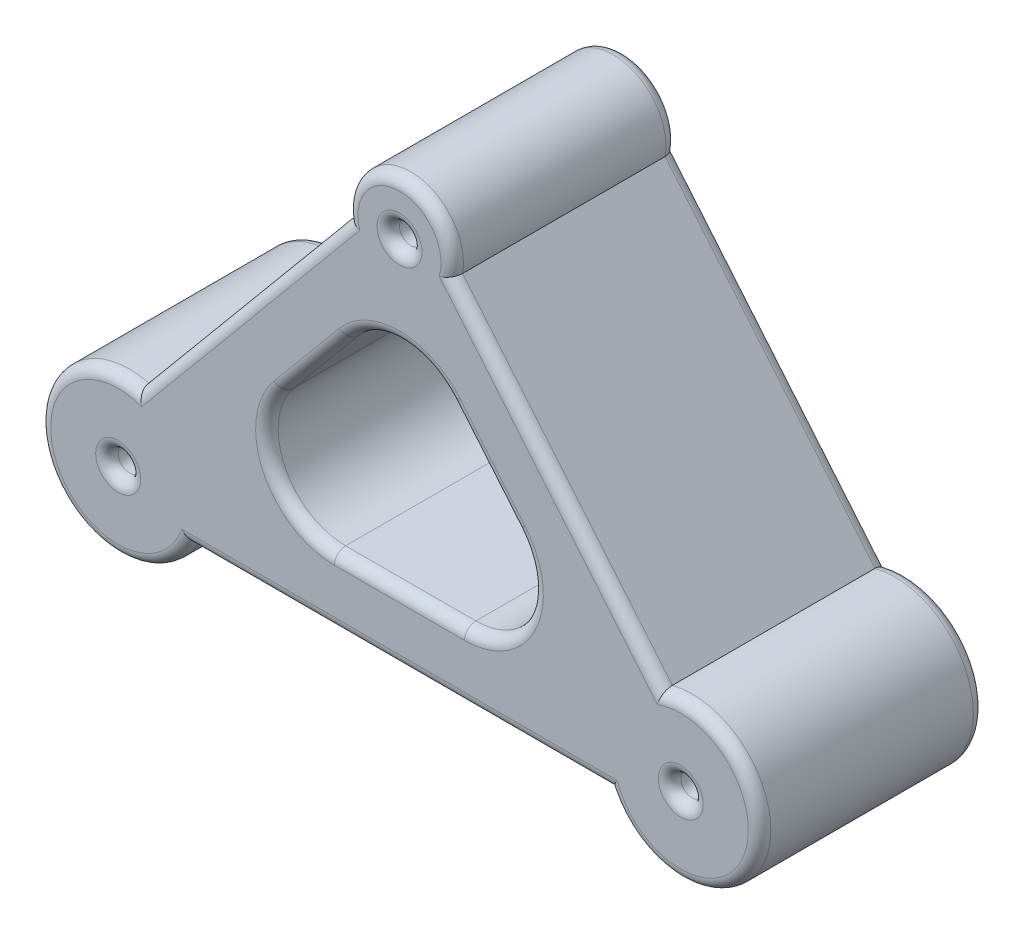
SolidWorks part; units mm, degrees
ref_plane "Front Plane" through (0, 0, 0) normal (0, 0, 1) x (1, 0, 0)
ref_plane "Top Plane" through (0, 0, 0) normal (0, 1, 0) x (1, 0, 0)
ref_plane "Right Plane" through (0, 0, 0) normal (1, 0, 0) x (0, 0, -1)
sketch "Esquisse1" plane through (0, 0, 0) normal (0, 0, 1) x (1, 0, 0)
  line L0 (0, 0) -> (0, 15) construction
  line L1 (-11.6279, 3.3896) -> (-2.3047, 14.5775)
  line L2 (-12.5, 0) -> (0, 15) construction
  line L3 (-5.197, 6.4206) -> (-2.3047, 9.8913)
  line L4 (-12.5, 0) -> (0, 0) construction
  line L5 (2.8923, 1.5) -> (-2.8923, 1.5)
  line L6 (9.3377, -1.5) -> (-9.3377, -1.5)
  line L7 (0, 15) -> (12.5, 0) construction
  line L8 (12.5, 0) -> (0, 0) construction
  line L9 (5.197, 6.4206) -> (2.3047, 9.8913)
  line L11 (2.3047, 14.5775) -> (11.6279, 3.3896)
  circle A0 centre (-12.5, 0) radius 0.5
  arc A2 (2.3047, 14.5775) -> (-2.3047, 14.5775) centre (0, 15) ccw
  circle A3 centre (0, 15) radius 0.5
  circle A5 centre (12.5, 0) radius 0.5
  arc A8 (-11.6279, 3.3896) -> (-9.3377, -1.5) centre (-12.5, 0) ccw
  arc A9 (2.8923, 1.5) -> (5.197, 6.4206) centre (2.8923, 4.5) ccw
  arc A10 (-2.8923, 1.5) -> (-5.197, 6.4206) centre (-2.8923, 4.5) cw
  arc A11 (-2.3047, 9.8913) -> (2.3047, 9.8913) centre (0, 7.9708) cw
  arc A12 (11.6279, 3.3896) -> (9.3377, -1.5) centre (12.5, 0) cw
  point P24 (0, 12.6569)
  dimension "D1" = 1
  dimension "D2" = 25
  dimension "D3" = 3.5
  dimension "D7" = 3
  dimension "D4" = 15
  dimension "D5" = 3
  dimension "D6" = 3
extrude "Boss.-Extru.1" add sketch "Esquisse1" along normal mid plane 10
fillet "Congé2" radius 0.5 30 edges at (13, 0, 5) (0.5, 15, 5) (3.7508, 8.1559, 5) (0, 10.9708, 5) (-3.7508, 8.1559, 5) (-5.6091, 3.2275, 5) (0, 1.5, 5) (5.6091, 3.2275, 5) (0, -1.5, 5) (-15.6696, -1.4845, 5) (-6.9663, 8.9835, 5) (0, 17.3431, 5) (6.9663, 8.9835, 5) (15.6696, -1.4845, 5) (-12, 0, 5) (13, 0, -5) (-5.6091, 3.2275, -5) (-3.7508, 8.1559, -5) (0, 10.9708, -5) (3.7508, 8.1559, -5) (5.6091, 3.2275, -5) (0, 1.5, -5) (-12, 0, -5) (6.9663, 8.9835, -5) (0, 17.3431, -5) (-6.9663, 8.9835, -5) (-15.6696, -1.4845, -5) (0, -1.5, -5) (15.6696, -1.4845, -5) (0.5, 15, -5)
